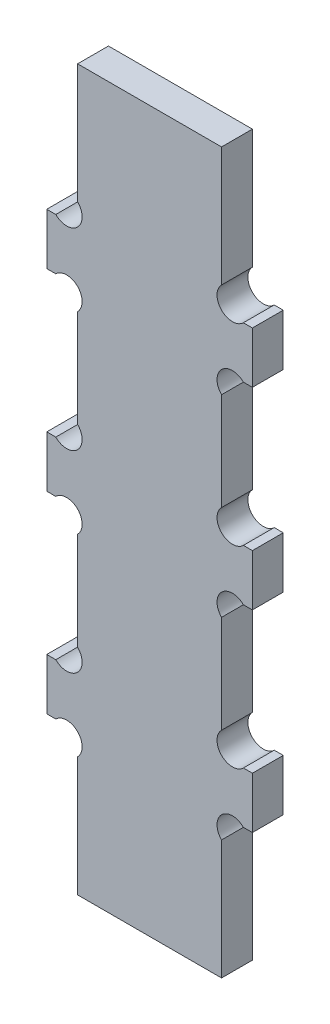
SolidWorks part; units mm, degrees
ref_plane "Alzado" through (0, 0, 0) normal (0, 0, 1) x (1, 0, 0)
ref_plane "Planta" through (0, 0, 0) normal (0, 1, 0) x (1, 0, 0)
ref_plane "Vista lateral" through (0, 0, 0) normal (1, 0, 0) x (0, 0, -1)
sketch "Croquis1" plane through (0, 0, 0) normal (0, 0, 1) x (1, 0, 0)
  line L1 (-10, -35) -> (10, -35)
  line L2 (-10, -35) -> (-10, 35)
  line L3 (-10, 35) -> (10, 35)
  line L4 (10, -35) -> (10, 35)
  line L5 (-10, -35) -> (10, 35) construction
  line L6 (-10, 35) -> (10, -35) construction
  point P0 (0, 0)
  dimension "D1" = 20
  dimension "D2" = 70
extrude "Saliente-Extruir1" add sketch "Croquis1" along normal blind 3
sketch "Croquis2" plane through (0, 0, 3) normal (0, 0, 1) x (1, 0, 0)
  line L0 (10, -35) -> (10, 35) construction
  line L2 (10, 35) -> (7, 35)
  line L4 (10, 35) -> (10, 21.25)
  line L5 (10, 21.25) -> (7, 21.25)
  line L6 (7, 35) -> (7, 21.25)
  line L7 (10, 16.25) -> (7, 16.25)
  line L8 (10, 16.25) -> (10, 2.5)
  line L9 (10, 2.5) -> (7, 2.5)
  line L10 (7, 16.25) -> (7, 2.5)
  line L12 (10, -21.25) -> (7, -21.25)
  line L13 (10, -21.25) -> (10, -35)
  line L14 (10, -35) -> (7, -35)
  line L16 (7, -21.25) -> (7, -35)
  line L17 (10, -2.5) -> (7, -2.5)
  line L18 (10, -2.5) -> (10, -16.25)
  line L19 (10, -16.25) -> (7, -16.25)
  line L20 (7, -2.5) -> (7, -16.25)
  line L21 (7, 21.25) -> (7, 16.25) construction
  line L22 (7, 2.5) -> (7, -2.5) construction
  line L23 (7, -16.25) -> (7, -21.25) construction
  line L24 (-10, -35) -> (10, -35) construction
  line L25 (0, 35) -> (0, 0) construction
  line L26 (10, 35) -> (-10, 35) construction
  line L27 (-7, -16.25) -> (-7, -21.25) construction
  line L28 (-7, 2.5) -> (-7, -2.5) construction
  line L29 (-7, 21.25) -> (-7, 16.25) construction
  line L30 (-7, -2.5) -> (-7, -16.25)
  line L31 (-10, -16.25) -> (-7, -16.25)
  line L32 (-10, -2.5) -> (-10, -16.25)
  line L33 (-10, -2.5) -> (-7, -2.5)
  line L34 (-7, -21.25) -> (-7, -35)
  line L35 (-10, -35) -> (-7, -35)
  line L36 (-10, -21.25) -> (-10, -35)
  line L37 (-10, -21.25) -> (-7, -21.25)
  line L38 (-7, 16.25) -> (-7, 2.5)
  line L39 (-10, 2.5) -> (-7, 2.5)
  line L40 (-10, 16.25) -> (-10, 2.5)
  line L41 (-10, 16.25) -> (-7, 16.25)
  line L42 (-7, 35) -> (-7, 21.25)
  line L43 (-10, 21.25) -> (-7, 21.25)
  line L44 (-10, 35) -> (-10, 21.25)
  line L45 (-10, 35) -> (-7, 35)
  dimension "D1" = 3
  dimension "D2" = 5
extrude "Cortar-Extruir1" cut sketch "Croquis2" against normal through all
sketch "Croquis3" plane through (0, 0, 3) normal (0, 0, 1) x (1, 0, 0)
  line L0 (10, 18.75) -> (4.5903, 18.75) construction
  line L1 (10, 16.25) -> (10, 21.25) construction
  line L2 (7, 9.375) -> (-7, 9.375) construction
  line L3 (7, 16.25) -> (7, 2.5) construction
  line L4 (-7, 2.5) -> (-7, 16.25) construction
  line L5 (7, -9.375) -> (-7, -9.375) construction
  line L6 (7, -2.5) -> (7, -16.25) construction
  line L7 (-7, -16.25) -> (-7, -2.5) construction
  line L8 (0, 35) -> (0, 9.375) construction
  line L9 (7, 35) -> (-7, 35) construction
  line L10 (7, 21.25) -> (8.5, 22.75) construction
  line L11 (7, 21.25) -> (10, 21.25) construction
  line L12 (7, 35) -> (7, 21.25) construction
  circle A0 centre (8.5, 22.75) radius 1.5 construction
  circle A1 centre (8.0607, 22.3107) radius 1.5
  circle A2 centre (8.0607, 15.1893) radius 1.5
  circle A3 centre (8.0607, 3.5607) radius 1.5
  circle A4 centre (8.0607, -3.5607) radius 1.5
  circle A5 centre (8.0607, -15.1893) radius 1.5
  circle A6 centre (8.0607, -22.3107) radius 1.5
  circle A7 centre (-8.0607, -22.3107) radius 1.5
  circle A8 centre (-8.0607, -15.1893) radius 1.5
  circle A9 centre (-8.0607, -3.5607) radius 1.5
  circle A10 centre (-8.0607, 3.5607) radius 1.5
  circle A11 centre (-8.0607, 15.1893) radius 1.5
  circle A12 centre (-8.0607, 22.3107) radius 1.5
  dimension "D1" = 3
extrude "Cortar-Extruir2" cut sketch "Croquis3" against normal through all
